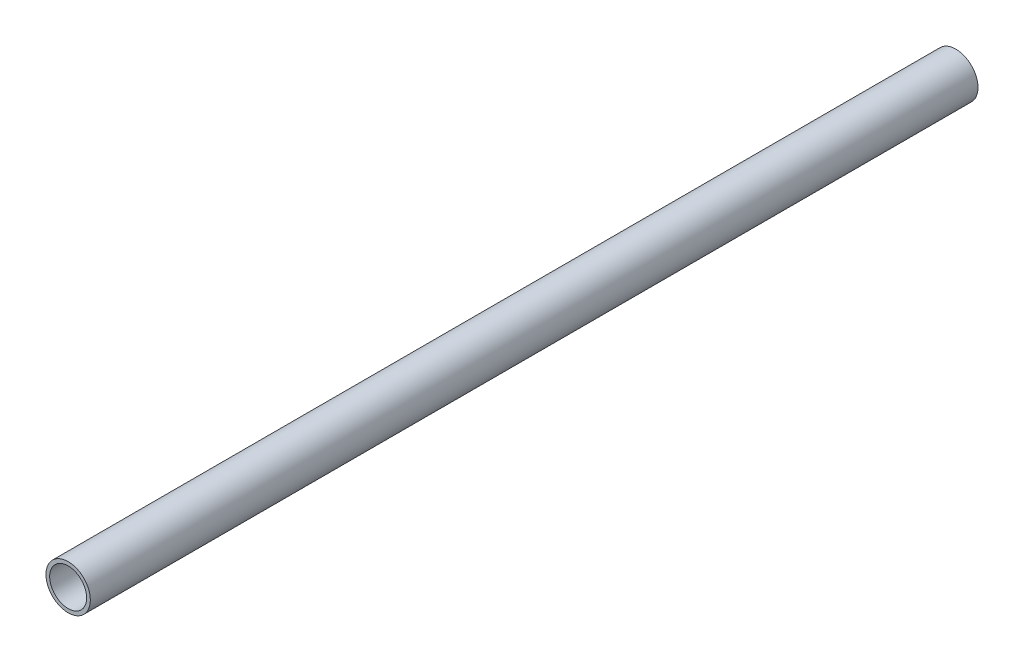
SolidWorks part; units mm, degrees
ref_plane "Front Plane" through (0, 0, 0) normal (0, 0, 1) x (1, 0, 0)
ref_plane "Top Plane" through (0, 0, 0) normal (0, 1, 0) x (1, 0, 0)
ref_plane "Right Plane" through (0, 0, 0) normal (1, 0, 0) x (0, 0, -1)
sketch "Sketch1" plane through (0, 0, 0) normal (0, 0, 1) x (1, 0, 0)
  circle A0 centre (0, 0) radius 10
  circle A1 centre (0, 0) radius 12
  dimension "D1" = 20
  dimension "D2" = 2
extrude "Boss-Extrude1" add sketch "Sketch1" along normal blind 480
